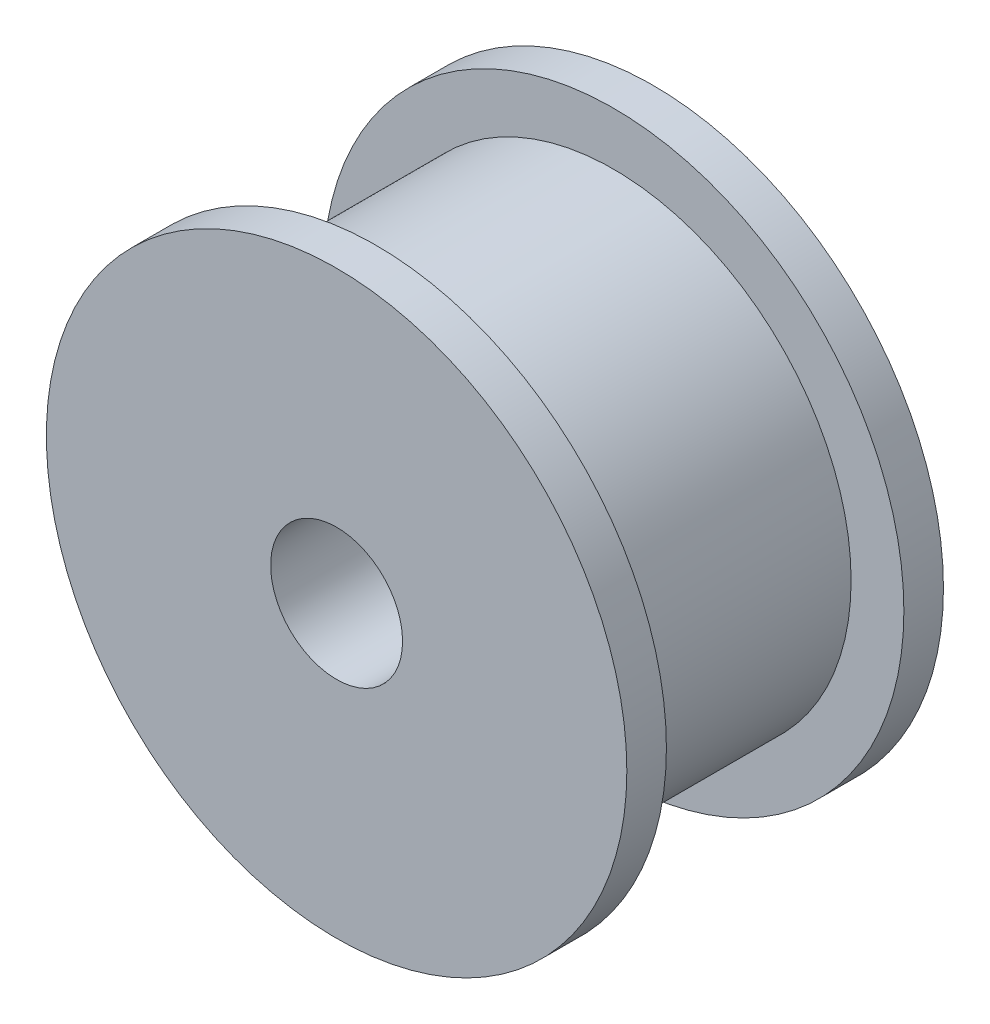
SolidWorks part; units mm, degrees
ref_plane "Plan de face" through (0, 0, 0) normal (0, 0, 1) x (1, 0, 0)
ref_plane "Plan de dessus" through (0, 0, 0) normal (0, 1, 0) x (1, 0, 0)
ref_plane "Plan de droite" through (0, 0, 0) normal (1, 0, 0) x (0, 0, -1)
sketch "Esquisse1" plane through (0, 0, 0) normal (0, 0, 1) x (1, 0, 0)
  circle A0 centre (0, 0) radius 11
  dimension "D1" = 22
extrude "Boss.-Extru.1" add sketch "Esquisse1" along normal blind 1.5
sketch "Esquisse2" plane through (0, 0, 1.5) normal (0, 0, 1) x (1, 0, 0)
  circle A0 centre (0, 0) radius 9
  dimension "D1" = 18
extrude "Boss.-Extru.2" add sketch "Esquisse2" along normal blind 9
sketch "Esquisse3" plane through (0, 0, 10.5) normal (0, 0, 1) x (1, 0, 0)
  circle A0 centre (0, 0) radius 11
extrude "Boss.-Extru.3" add sketch "Esquisse3" along normal blind 1.5
sketch "Esquisse4" plane through (0, 0, 12) normal (0, 0, 1) x (1, 0, 0)
  circle A0 centre (0, 0) radius 2.5
  dimension "D1" = 5
extrude "Enlèv. mat.-Extru.1" cut sketch "Esquisse4" against normal through all and the other way through all
